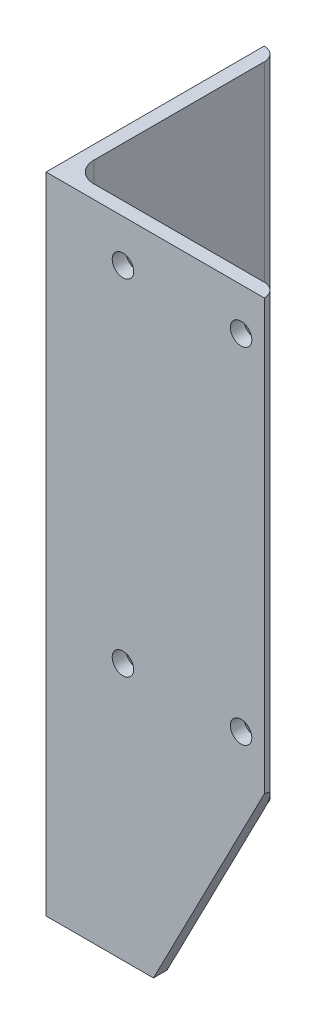
SolidWorks part; units mm, degrees
ref_plane "Alzado" through (0, 0, 0) normal (0, 0, 1) x (1, 0, 0)
ref_plane "Planta" through (0, 0, 0) normal (0, 1, 0) x (1, 0, 0)
ref_plane "Vista lateral" through (0, 0, 0) normal (1, 0, 0) x (0, 0, -1)
sketch "Croquis1" plane through (0, 0, 0) normal (0, 0, 1) x (1, 0, 0)
  line L0 (0, 0) -> (0, 150)
  dimension "D1" = 150
other "Hierro angular 2 X 2 X 0.125(1)"
ref_plane "Plano1" through (0, 0, 0) normal (0, 1, 0) x (1, 0, 0)
sketch "Sketch1" plane through (0, 0, 0) normal (0, 1, 0) x (1, 0, 0)
  line L0 (0, 0) -> (0, 50.8)
  line L1 (0, 50.8) -> (0.0051, 50.8)
  line L2 (3.175, 47.6301) -> (3.175, 7.9375)
  line L3 (7.9375, 3.175) -> (47.6301, 3.175)
  line L4 (50.8, 0.0051) -> (50.8, 0)
  line L5 (50.8, 0) -> (0, 0)
  arc A0 (50.8, 0.0051) -> (47.6301, 3.175) centre (47.6301, 0.0051) ccw
  arc A1 (0.0051, 50.8) -> (3.175, 47.6301) centre (0.0051, 47.6301) cw
  arc A2 (7.9375, 3.175) -> (3.175, 7.9375) centre (7.9375, 7.9375) cw
  point P10 (25.4, 0)
  point P14 (0, 25.4)
  point P15 (3.175, 25.4)
  point P16 (25.4, 3.175)
  point P17 (3.175, 50.8)
  point P18 (50.8, 3.175)
  point P19 (0, 0)
  dimension "D2" = 0.0051
  dimension "Radius_1" = 4.7625
  dimension "D1" = 3.175
  dimension "H_leg" = 50.8
sketch "Croquis3" plane through (0, 0, 0) normal (0, 0, 1) x (1, 0, 0)
  line L0 (0, 50) -> (50.8, 50) construction
  line L3 (0, 0) -> (0, 150) construction
  line L4 (50.8, 150) -> (50.8, 0) construction
  line L5 (0, 150) -> (50.8, 150) construction
  line L6 (25, 50) -> (25, 0) construction
  line L7 (0, 0) -> (50.8, 0) construction
  line L8 (25, 0) -> (50.8, 50)
  line L9 (50.8, 50) -> (50.8, 0)
  line L10 (50.8, 0) -> (25, 0)
  dimension "D1" = 100
  dimension "D2" = 25
extrude "Cortar-Extruir1" cut sketch "Croquis3" against normal blind 10
sketch "Croquis4" plane through (0, 0, 0) normal (0, 0, 1) x (1, 0, 0)
  line L0 (50.8, 150) -> (50.8, 50) construction
  line L1 (45.4, 140.12) -> (17.9, 140.12) construction
  line L2 (45.4, 140.12) -> (45.4, 59.87) construction
  line L3 (45.4, 59.87) -> (17.9, 59.87) construction
  line L4 (17.9, 140.12) -> (17.9, 59.87) construction
  line L5 (0, 150) -> (50.8, 150) construction
  circle A0 centre (17.9, 140.12) radius 2.5
  circle A1 centre (45.4, 140.12) radius 2.5
  circle A2 centre (17.9, 59.87) radius 2.5
  circle A3 centre (45.4, 59.87) radius 2.5
  dimension "D5" = 5
  dimension "D1" = 5.4
  dimension "D2" = 9.88
  dimension "D3" = 27.5
  dimension "D4" = 80.25
extrude "Cortar-Extruir2" cut sketch "Croquis4" against normal up to surface (3.175 mm away) up to face at (27.227, 68.7713, -3.175)
